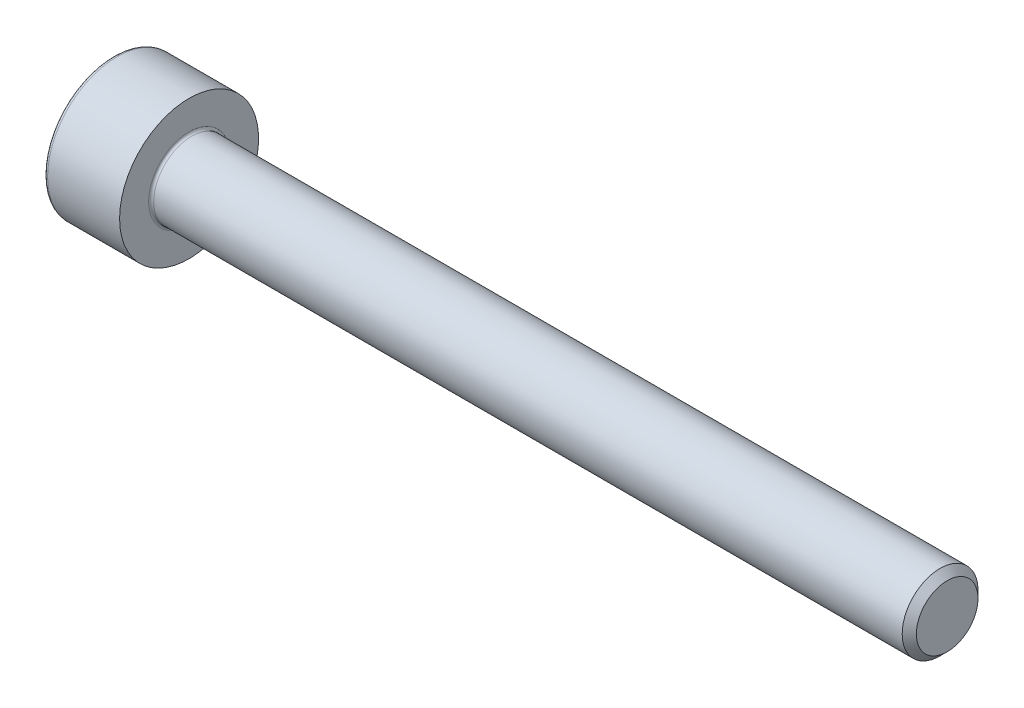
SolidWorks part; units mm, degrees
ref_plane "Plane1" through (0, 0, 0) normal (0, 0, 1) x (1, 0, 0)
ref_plane "Plane2" through (0, 0, 0) normal (0, 1, 0) x (1, 0, 0)
ref_plane "Plane3" through (0, 0, 0) normal (1, 0, 0) x (0, 0, -1)
sketch "BodySke" plane through (0, 0, 0) normal (0, 0, 1) x (1, 0, 0)
  line L0 (0, 0) -> (0, 2.75)
  line L1 (0, 2.75) -> (3, 2.75)
  line L2 (3, 2.75) -> (3, 1.5)
  line L3 (3, 1.5) -> (32.7195, 1.5)
  line L4 (33, 1.2195) -> (33, 0)
  line L5 (33, 0) -> (0, 0)
  line L6 (-31.75, 0) -> (127, 0) construction
  line L8 (33, 1.2195) -> (32.7195, 1.5)
  line L10 (33, -1.2195) -> (32.7195, -1.5) construction
  line L11 (3.5, 9.525) -> (3.5, 3.175) construction
  line L12 (15, 9.525) -> (15, 3.175) construction
  line L13 (-27, 9.525) -> (-27, 3.175) construction
  dimension "Diameter" = 3
  dimension "Head_ht" = 3
  dimension "Length" = 30
  dimension "Body_ch_ang" = 45
  dimension "Head_dia" = 5.5
  dimension "Minor_dia" = 2.439
  dimension "Advance" = 0.5
  dimension "Thread_nom" = 18
  dimension "Thread_length" = 60
revolve "Base-Revolve" add sketch "BodySke"
cosmetic thread "ThreadCosmetic" [suppressed]
fillet "Fillet1" radius 0.1 1 edges at (3, 0, 1.5)
fillet "Fillet2" radius 0.15 1 edges at (0, 0, 2.75)
sketch "Sketch2" plane through (0, 0, 0) normal (0, 0, 1) x (1, 0, 0)
  line L0 (0, 1.28) -> (1.3, 1.28)
  line L1 (1.3, 1.28) -> (2.039, 0)
  line L2 (-31.75, 0) -> (127, 0) construction
  line L3 (2.039, 0) -> (0, 0)
  line L4 (0, 0) -> (0, 1.28)
  line L6 (0, 0) -> (47.625, 0) construction
  dimension "D1" = 1.28
  dimension "D2" = 60
  dimension "Depth" = 1.3
revolve "Hex-PreBroach" cut sketch "Sketch2" angle 360 about L6
sketch "Sketch3" plane through (0, 0, 0) normal (-1, 0, 0) x (0, 0.5, 0.866)
  line L0 (0.739, 1.28) -> (-0.739, 1.28)
  line L1 (-0.739, 1.28) -> (-1.478, 0)
  line L2 (0.739, 1.28) -> (1.478, 0)
  line L3 (0.739, -1.28) -> (1.478, 0)
  line L4 (0.739, -1.28) -> (-0.739, -1.28)
  line L5 (-0.739, -1.28) -> (-1.478, 0)
  dimension "D1" = 1.28
  dimension "D2" = 1.28
  dimension "Hex_size" = 2.56
extrude "Hex" cut sketch "Sketch3" against normal blind 1.3
sketch "ThdSchSke" plane through (0, 0, 0) normal (0, 0, 1) x (1, 0, 0)
  line L0 (15, -1.2195) -> (14.8036, -1.5)
  line L1 (15, -1.2195) -> (15.1964, -1.5)
  line L2 (15.1964, -1.5) -> (15.1964, -1.875)
  line L3 (-3.175, 0) -> (5.1513, 0) construction
  line L4 (0, 2.6) -> (0, -2.6) construction
  line L5 (15.1964, -1.875) -> (14.8036, -1.875)
  line L6 (14.8036, -1.875) -> (14.8036, -1.5)
  dimension "Thread_minor" = 2.439
  dimension "Diameter" = 3
  dimension "Start" = 15
  dimension "SideAngle" = 55
  dimension "VeeAngle" = 70
  dimension "Overcut" = 3.75
revolve "ThreadSchematic" [suppressed] cut sketch "ThdSchSke" angle 360 about L3
pattern_linear "ThdSchPat" [suppressed]
equation "\"D2@Sketch3\" = \"Hex_size@Sketch3\" / 2"
equation "\"D1@Sketch3\" = \"Hex_size@Sketch3\" / 2"
equation "\"D1@Sketch2\" = \"Hex_size@Sketch3\" / 2"
equation "\"Thread_minor@ThreadCosmetic\"  =  \"Minor_dia@BodySke\""
equation "\"Depth@Sketch2\" =  \"Key_eng@Hex\""
equation "\"Thread_length@ThreadCosmetic\" = ((sgn( (\"Length@BodySke\" - \"Advance@BodySke\" * 3.0) - \"Thread_nom@BodySke\" )-1)*( (\"Length@BodySke\" - \"Advance@BodySke\" * 3.0) - \"Thread_nom@BodySke\" ))/-2+ \"Thread_nom@BodySke\""
equation "\"Thread_minor@ThdSchSke\" = \"Minor_dia@BodySke\""
equation "\"Diameter@ThdSchSke\" = \"Diameter@BodySke\""
equation "\"Overcut@ThdSchSke\" = \"Diameter@BodySke\" * 1.25"
equation "\"Start@ThdSchSke\" = \"Head_ht@BodySke\" + \"Length@BodySke\" - \"Thread_length@ThreadCosmetic\"  '---Non-countersunk---"
equation "\"Num_threads@ThdSchPat\" = int( \"Thread_length@ThreadCosmetic\" / \"Advance@BodySke\" + 0.999 )  + 1"
equation "\"Advance@ThdSchPat\" = \"Thread_length@ThreadCosmetic\" /  (\"Num_threads@ThdSchPat\" - 1) 'relax it"
equation "\"Num_threads@ThdSchPat\" = \"Num_threads@ThdSchPat\" - sgn( \"Num_threads@ThdSchPat\" - 1) '---chamfered tips only---"
